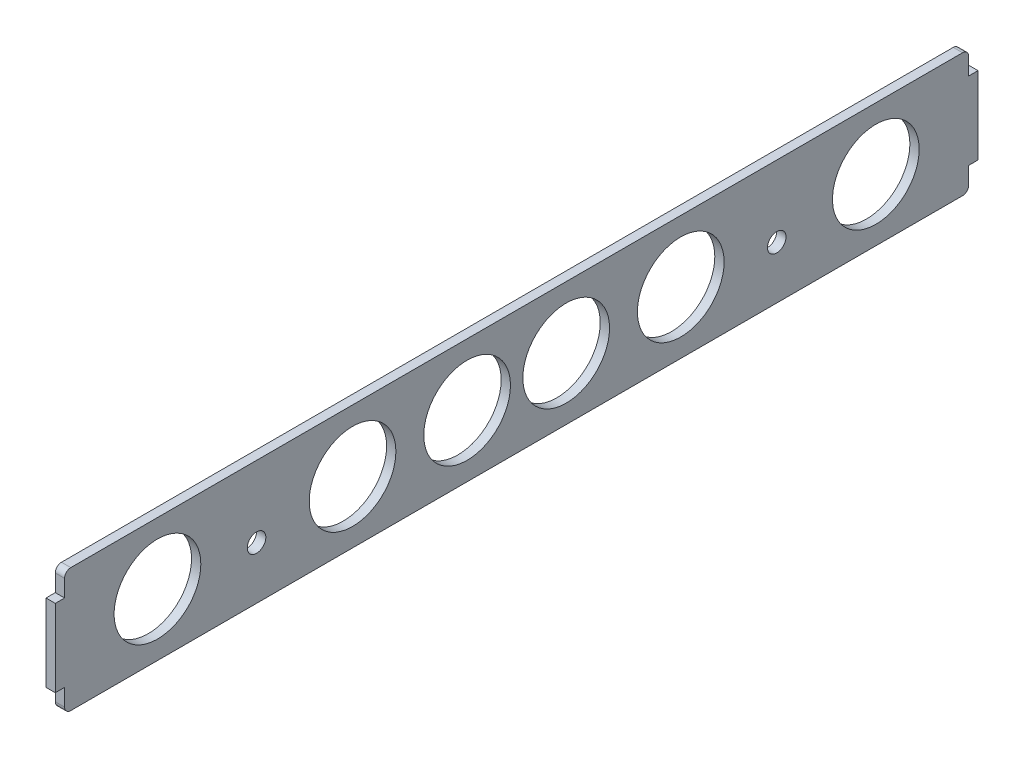
SolidWorks part; units mm, degrees
ref_plane "Front Plane" through (0, 0, 0) normal (0, 0, 1) x (1, 0, 0)
ref_plane "Top Plane" through (0, 0, 0) normal (0, 1, 0) x (1, 0, 0)
ref_plane "Right Plane" through (0, 0, 0) normal (1, 0, 0) x (0, 0, -1)
sketch "Sketch3" plane through (0, 0, 0) normal (1, 0, 0) x (0, 0, -1)
  line L1 (0, 0) -> (292, 0)
  line L2 (0, 0) -> (0, -40)
  line L3 (0, -40) -> (292, -40)
  line L4 (292, 0) -> (292, -40)
  line L5 (22.5, 0) -> (47.5, 0) construction
  line L6 (22.5, 0) -> (22.5, 3) construction
  line L7 (22.5, 3) -> (47.5, 3) construction
  line L8 (47.5, 0) -> (47.5, 3) construction
  line L9 (244.5, 0) -> (269.5, 0) construction
  line L10 (244.5, 0) -> (244.5, 3) construction
  line L11 (244.5, 3) -> (269.5, 3) construction
  line L12 (269.5, 0) -> (269.5, 3) construction
  line L13 (0, -9) -> (3, -9) construction
  line L14 (0, -9) -> (0, -31) construction
  line L15 (0, -31) -> (3, -31) construction
  line L16 (3, -9) -> (3, -31) construction
  line L17 (292, -9) -> (289, -9) construction
  line L18 (292, -9) -> (292, -31) construction
  line L19 (292, -31) -> (289, -31) construction
  line L20 (289, -9) -> (289, -31) construction
  line L21 (66.04, -9) -> (69.04, -9) construction
  line L22 (66.04, -9) -> (66.04, -31) construction
  line L23 (66.04, -31) -> (69.04, -31) construction
  line L24 (69.04, -9) -> (69.04, -31) construction
  line L25 (222.96, -9) -> (225.96, -9) construction
  line L26 (222.96, -9) -> (222.96, -31) construction
  line L27 (222.96, -31) -> (225.96, -31) construction
  line L28 (225.96, -9) -> (225.96, -31) construction
  circle A0 centre (62, -23) radius 3
  circle A1 centre (230, -23) radius 3
  point P29 (67.54, -9)
  point P30 (224.46, -9)
  point P32 (3, -20)
  point P33 (69.04, -20)
  point P34 (225.96, -20)
  point P35 (289, -20)
  point P36 (292, -20)
  point P37 (66.04, -20)
  point P38 (35, 3)
  point P39 (257, 3)
  point P42 (0, -20)
  dimension "D14" = 6
  dimension "D16" = 6
  dimension "D1" = 40
  dimension "D2" = 292
  dimension "D3" = 67.54
  dimension "D4" = 67.54
  dimension "D5" = 25
  dimension "D6" = 25
  dimension "D7" = 3
  dimension "D8" = 22
  dimension "D9" = 22
  dimension "D10" = 22
  dimension "D11" = 22
  dimension "D12" = 35
  dimension "D13" = 35
  dimension "D15" = 62
  dimension "D17" = 62
  dimension "D18" = 3
extrude "Boss-Extrude2" add sketch "Sketch3" along normal blind 3 contours L20 L17 L4 L1 L2 L13 L16 L15 L3 L19 L21 L24 L23 L22 L25 L28 L27 L26 | L1 L8 L7 L6 | L1 L12 L11 L10
fillet "Fillet1" radius 2 4 edges at (1.5, 0, -292) (1.5, -40, -292) (1.5, -40, 0) (1.5, 0, 0)
sketch "Sketch4" plane through (3, 0, 0) normal (1, 0, 0) x (0, 0, -1)
  line L0 (0, -20) -> (307.4873, -20) construction
  line L1 (0, -2) -> (0, -38) construction
  line L2 (292, -2) -> (292, -38) construction
  circle A0 centre (30, -20) radius 14
  circle A1 centre (93, -20) radius 14
  circle A2 centre (130, -20) radius 14
  circle A3 centre (162, -20) radius 14
  circle A4 centre (199, -20) radius 14
  circle A5 centre (262, -20) radius 14
  dimension "D1" = 28
  dimension "D3" = 30
  dimension "D2" = 30
  dimension "D4" = 93
  dimension "D5" = 93
  dimension "D6" = 130
  dimension "D7" = 130
extrude "Cut-Extrude1" cut sketch "Sketch4" against normal blind 10
sketch "Sketch5" plane through (3, 0, 0) normal (1, 0, 0) x (0, 0, -1)
  line L0 (0, -2) -> (0, -38) construction
  line L1 (0, -7.5) -> (-3, -7.5)
  line L2 (0, -7.5) -> (0, -32.5)
  line L3 (0, -32.5) -> (-3, -32.5)
  line L4 (-3, -7.5) -> (-3, -32.5)
  line L5 (292, -2) -> (292, -38) construction
  line L6 (292, -7.5) -> (295, -7.5)
  line L7 (292, -7.5) -> (292, -32.5)
  line L8 (292, -32.5) -> (295, -32.5)
  line L9 (295, -7.5) -> (295, -32.5)
  point P12 (295, -20)
  point P13 (-3, -20)
  point P14 (0, -20)
  dimension "D1" = 25
  dimension "D2" = 3
extrude "Boss-Extrude3" add sketch "Sketch5" against normal blind 3
equation "\"D4@Sketch3\"=\"D3@Sketch3\""
equation "\"D6@Sketch3\"=\"D5@Sketch3\""
